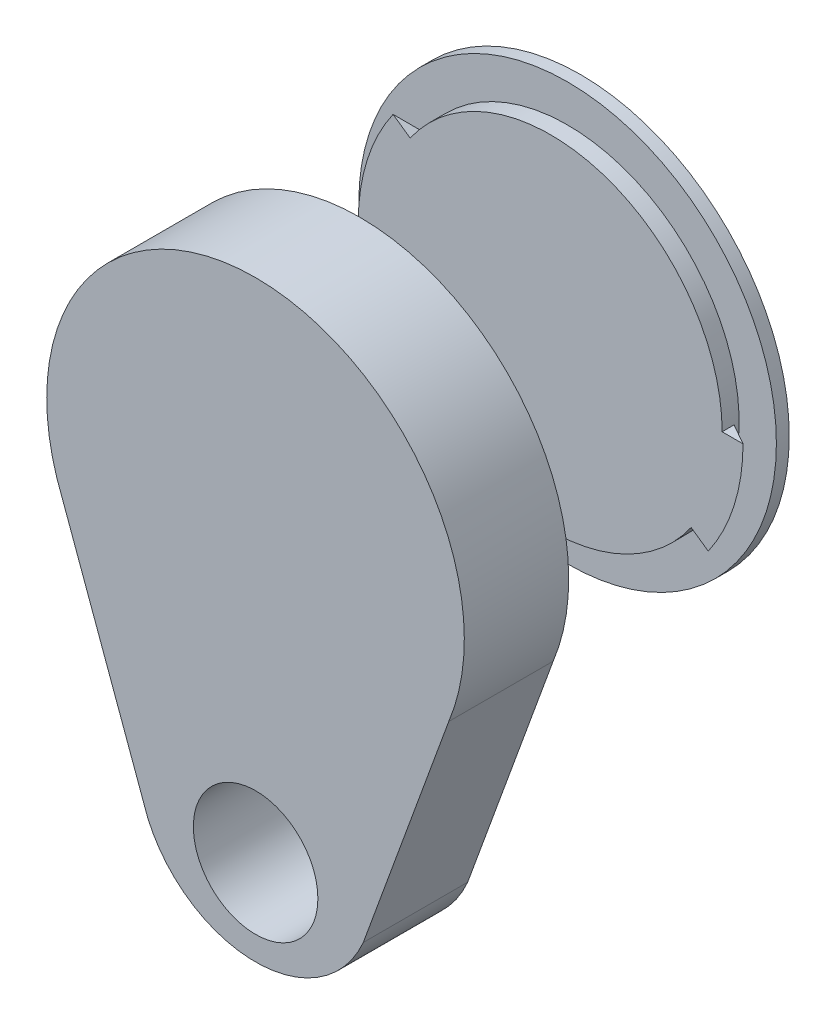
SolidWorks part; units mm, degrees
ref_plane "Plan de face" through (0, 0, 0) normal (0, 0, 1) x (1, 0, 0)
ref_plane "Plan de dessus" through (0, 0, 0) normal (0, 1, 0) x (1, 0, 0)
ref_plane "Plan de droite" through (0, 0, 0) normal (1, 0, 0) x (0, 0, -1)
sketch "Esquisse1" plane through (1.309, 0, 0) normal (0, 1, 0) x (1, 0, 0)
  line L0 (0.2535, -3.046) -> (-13.7465, -3.046)
  line L1 (-13.7465, -3.046) -> (-13.7465, 3.954)
  line L2 (-13.7465, 3.954) -> (-12.7465, 3.954)
  line L4 (-12.7465, 3.954) -> (-12.7465, 3.4429)
  line L5 (-12.7465, 3.4429) -> (-12.7465, 2.954)
  line L6 (-12.7465, 2.954) -> (-12.7465, -2.046)
  line L7 (-12.7465, -2.046) -> (0.2535, -2.046)
  line L8 (0.2535, -2.046) -> (0.2535, -3.046)
  dimension "D1" = 14
  dimension "D2" = 1
  dimension "D3" = 1
  dimension "D4" = 7
  dimension "D5" = 5
  dimension "D8" = 1
revolve "Révolution1" add sketch "Esquisse1" angle 360 about L8
sketch "Esquisse2" plane through (0, 0, -11.8007) normal (0, 1, 0) x (1, 0, 0)
  line L0 (0.6636, 5.8413) -> (-10.8364, 5.8413)
  line L1 (-10.8364, 5.8413) -> (-10.8364, 6.3655)
  line L2 (-10.8364, 6.3655) -> (-10.8364, 6.9783)
  line L3 (-10.8364, 6.9783) -> (-13.3364, 6.9783)
  line L4 (-13.3364, 6.9783) -> (-13.3364, 7.8413)
  line L5 (-13.3364, 7.8413) -> (0.6636, 7.8413)
  line L6 (0.6636, 7.8413) -> (0.6636, 5.8413)
  dimension "D1" = 2
  dimension "D2" = 11.5
  dimension "D3" = 2.5
  dimension "D5" = 14
revolve "Révolution2" add sketch "Esquisse2" angle 360 about L6
ref_plane "Plan1" through (0, 0, 3.046) normal (0, 0, 1) x (1, 0, 0)
ref_plane "Plan2" through (0, 0, 2.046) normal (0, 0, 1) x (1, 0, 0)
sketch "Esquisse10" plane through (0, 0, 3.046) normal (0, 0, 1) x (1, 0, 0)
  line L0 (14.8888, -4.2906) -> (8.7888, -21)
  line L1 (-5.6638, -21) -> (-11.7638, -4.2906)
  line L2 (1.5625, 0) -> (-12.4375, 0) construction
  arc A0 (14.8888, -4.2906) -> (-11.7638, -4.2906) centre (1.5625, 1.1242) cw
  circle A1 centre (1.5625, 0) radius 14 construction
  arc A2 (8.7888, -21) -> (-5.6638, -21) centre (1.5625, -17.8753) cw
  dimension "D1" = 21
  dimension "D2" = 21
extrude "Boss.-Extru.4" add sketch "Esquisse10" against normal blind 7
sketch "Esquisse11" plane through (0, 0, 3.046) normal (0, 0, 1) x (1, 0, 0)
  circle A0 centre (1.5688, -19.9708) radius 4.1753
  arc A1 (-5.6638, -21) -> (8.7888, -21) centre (1.5625, -17.8753) ccw construction
  point P2 (1.5625, -25.7482)
  dimension "D1" = 5.7775
  dimension "D2" = 7.22
  dimension "D3" = 7.2326
extrude "Enlèv. mat.-Extru.2" cut sketch "Esquisse11" against normal blind 7
ref_axis "Axe1" through (0.6636, 0, -17.642) along (0, 0, -1)
sketch "Esquisse13" plane through (0, 0, 0) normal (0, 1, 0) x (1, 0, 0)
  line L0 (-10.8364, 17.642) -> (-12.2364, 17.642)
  line L1 (-12.2364, 17.642) -> (-10.8364, 18.442)
  line L2 (-10.8364, 18.779) -> (-10.8364, 17.642) construction
  line L3 (-10.8364, 18.442) -> (-10.8364, 17.642)
  dimension "D1" = 0.8
  dimension "D2" = 1.4
revolve "Révolution3" add sketch "Esquisse13" angle 35 about axis through (0.6636, 0, -17.642) along (0, 0, -1)
pattern_circular "Répétition circulaire1" count 2 over 360 about axis through (0.6636, 0, 0) along (0, 0, 1) of "Révolution3"
sketch "Esquisse14" plane through (0, 0, 0) normal (0, 1, 0) x (1, 0, 0)
  line L0 (-11.4375, 3.954) -> (-9.9375, 3.954)
  line L1 (15.5625, 3.954) -> (-12.4375, 3.954) construction
  line L2 (-9.9375, 3.954) -> (-11.4375, 3.154)
  line L4 (-11.4375, 3.154) -> (-11.4375, 3.954)
  dimension "D1" = 1.5
  dimension "D2" = 0.8
ref_axis "Axe2" through (1.5625, 0, 2.046) along (0, 0, -1)
revolve "Révolution4" add sketch "Esquisse14" angle 140 about axis through (1.5625, 0, 2.046) along (0, 0, -1)
pattern_circular "Répétition circulaire2" count 2 every 180 about axis through (1.5625, 0, 0) along (0, 0, 1) of "Révolution4"
equation "\"4.5.00mm\"=4"
